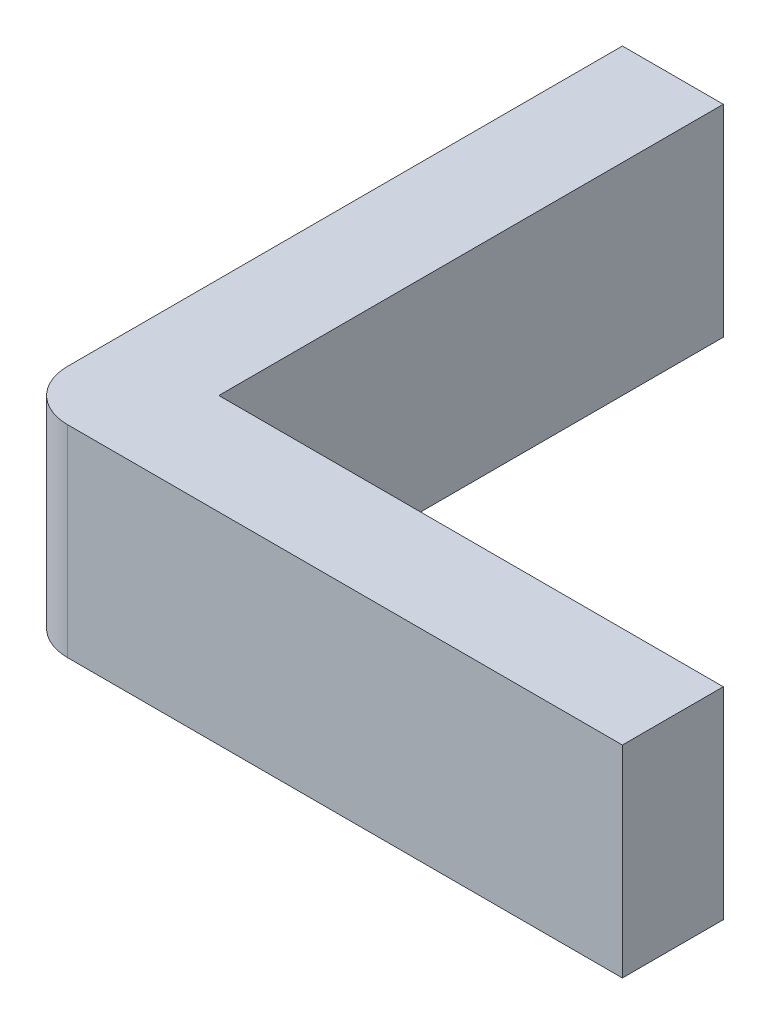
SolidWorks part; units mm, degrees
material "PVC Rigid"
ref_plane "Front Plane" through (0, 0, 0) normal (0, 0, 1) x (1, 0, 0)
ref_plane "Top Plane" through (0, 0, 0) normal (0, 1, 0) x (1, 0, 0)
ref_plane "Right Plane" through (0, 0, 0) normal (1, 0, 0) x (0, 0, -1)
sketch "Sketch1" plane through (0, 0, 0) normal (0, 1, 0) x (1, 0, 0)
  line L0 (0, 0) -> (12, 0)
  line L1 (12, 0) -> (12, 2)
  line L2 (12, 2) -> (2, 2)
  line L3 (2, 2) -> (2, 12)
  line L4 (2, 12) -> (0, 12)
  line L5 (0, 12) -> (0, 0)
extrude "Boss-Extrude1" add sketch "Sketch1" along normal blind 4
fillet "Fillet1" radius 1 1 edges at (0, 2, 0)
